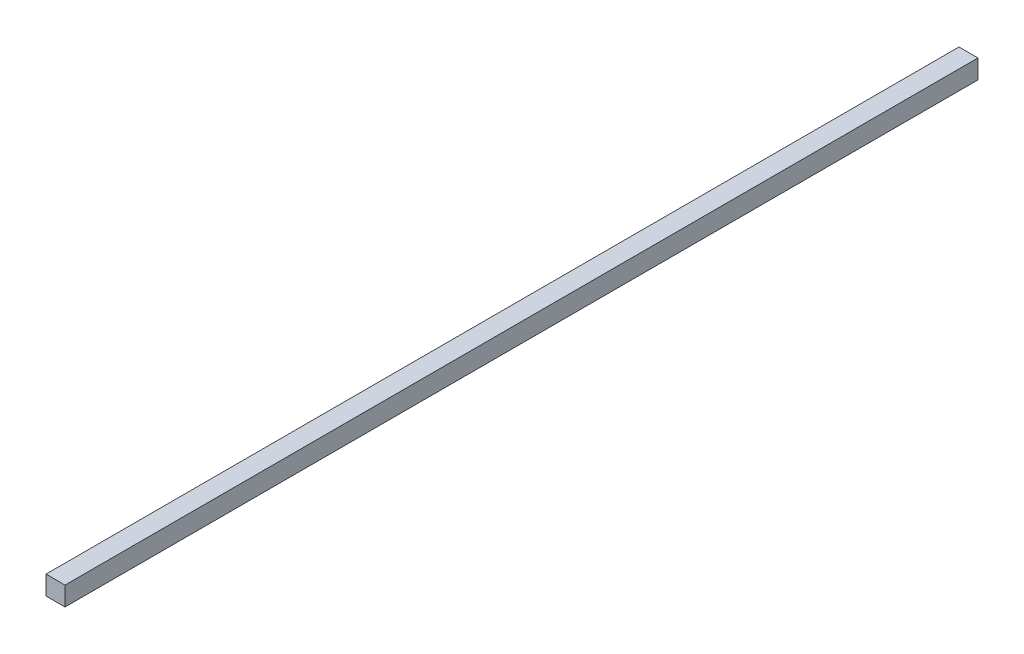
SolidWorks part; units mm, degrees
material "Oak"
ref_plane "Front Plane" through (0, 0, 0) normal (0, 0, 1) x (1, 0, 0)
ref_plane "Top Plane" through (0, 0, 0) normal (0, 1, 0) x (1, 0, 0)
ref_plane "Right Plane" through (0, 0, 0) normal (1, 0, 0) x (0, 0, -1)
sketch "Sketch1" plane through (0, 0, 0) normal (0, 0, 1) x (1, 0, 0)
  line L1 (0, 0) -> (-6.35, 0)
  line L2 (0, 0) -> (0, 6.35)
  line L3 (0, 6.35) -> (-6.35, 6.35)
  line L4 (-6.35, 0) -> (-6.35, 6.35)
  line L5 (0, 0) -> (-6.35, 6.35) construction
  line L6 (0, 6.35) -> (-6.35, 0) construction
  point P4 (-3.175, 3.175)
  dimension "D1" = 6.35
  dimension "D2" = 6.35
extrude "Boss-Extrude1" add sketch "Sketch1" along normal mid plane 304.8
